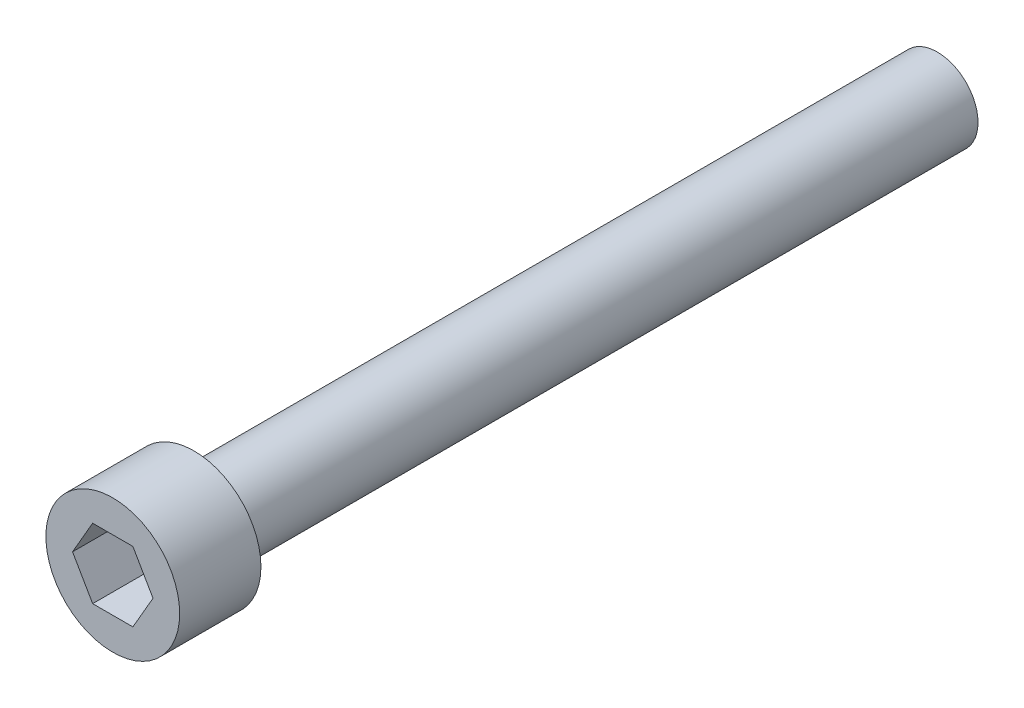
SolidWorks part; units mm, degrees
material "AISI 4340 Steel, normalized"
ref_plane "Front Plane" through (0, 0, 0) normal (0, 0, 1) x (1, 0, 0)
ref_plane "Top Plane" through (0, 0, 0) normal (0, 1, 0) x (1, 0, 0)
ref_plane "Right Plane" through (0, 0, 0) normal (1, 0, 0) x (0, 0, -1)
sketch "Sketch1" plane through (0, 0, 0) normal (0, 1, 0) x (1, 0, 0)
  line L0 (0, 0) -> (0, 42.2656)
  line L1 (0, 42.2656) -> (2.0828, 42.2656)
  line L2 (2.0828, 42.2656) -> (2.0828, 4.1656)
  line L3 (2.0828, 4.1656) -> (3.429, 4.1656)
  line L4 (3.429, 4.1656) -> (3.429, 0)
  line L5 (3.429, 0) -> (0, 0)
  dimension "D1" = 2.0828
  dimension "D2" = 3.429
  dimension "D3" = 4.1656
  dimension "D4" = 38.1
revolve "Revolve1" add sketch "Sketch1" angle 360 about L0
sketch "Sketch2" plane through (0, 0, 0) normal (0, 0, 1) x (1, 0, 0)
  line L1 (2.0622, 0) -> (1.0311, 1.7859)
  line L2 (1.0311, 1.7859) -> (-1.0311, 1.7859)
  line L3 (-1.0311, 1.7859) -> (-2.0622, 0)
  line L4 (-2.0622, 0) -> (-1.0311, -1.7859)
  line L5 (-1.0311, -1.7859) -> (1.0311, -1.7859)
  line L6 (1.0311, -1.7859) -> (2.0622, 0)
  circle A0 centre (0, 0) radius 1.7859 construction
  dimension "D1" = 3.5719
extrude "9-64 allen" cut sketch "Sketch2" against normal blind 3.175
